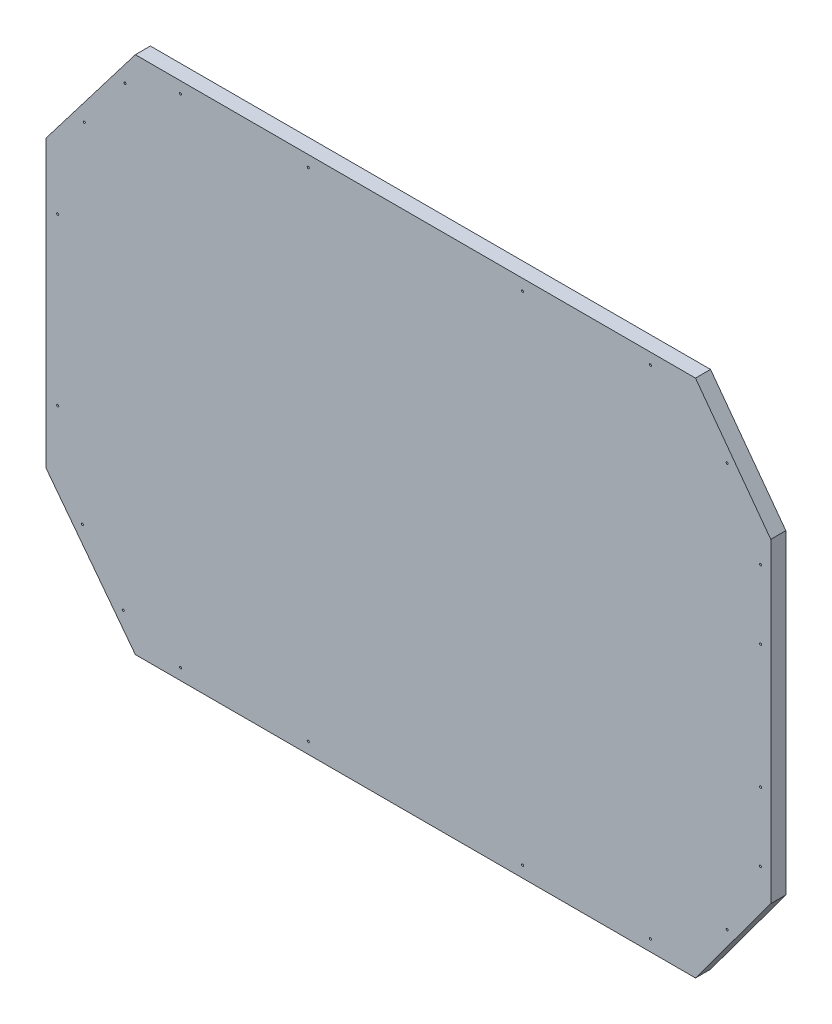
SolidWorks part; units mm, degrees
ref_plane "Front Plane" through (0, 0, 0) normal (0, 0, 1) x (1, 0, 0)
ref_plane "Top Plane" through (0, 0, 0) normal (0, 1, 0) x (1, 0, 0)
ref_plane "Right Plane" through (0, 0, 0) normal (1, 0, 0) x (0, 0, -1)
sketch "Sketch1" plane through (0, 0, 0) normal (0, 0, 1) x (1, 0, 0)
  line L0 (462.7979, 1011.4632) -> (442.7979, 1011.4632) construction
  line L1 (462.7979, 1036.4632) -> (462.7979, 1011.4632) construction
  line L2 (442.7979, 1036.4632) -> (442.7979, 1011.4632) construction
  line L3 (25, 700.8752) -> (25, 680.8752) construction
  line L4 (0, 700.8752) -> (25, 700.8752) construction
  line L5 (0, 680.8752) -> (25, 680.8752) construction
  line L6 (439.5826, 345.4877) -> (439.5826, 370.4877) construction
  line L7 (439.5826, 370.4877) -> (459.5826, 370.4877) construction
  line L8 (459.5826, 345.4877) -> (459.5826, 370.4877) construction
  line L9 (0, 500.6804) -> (118.58, 345.4877) construction
  line L10 (0, 881.2704) -> (0, 500.6804) construction
  line L11 (118.58, 1036.4632) -> (0, 881.2704) construction
  line L12 (863.58, 1036.4632) -> (118.58, 1036.4632) construction
  line L13 (863.58, 1036.4632) -> (963.71, 900.8043) construction
  line L14 (963.71, 900.8043) -> (963.71, 481.1465) construction
  line L15 (963.71, 481.1465) -> (863.58, 345.4877) construction
  line L16 (118.58, 345.4877) -> (863.58, 345.4877) construction
  line L17 (462.7979, 1011.4632) -> (442.7979, 1011.4632)
  line L18 (462.7979, 1036.4632) -> (462.7979, 1011.4632)
  line L19 (442.7979, 1036.4632) -> (442.7979, 1011.4632)
  line L20 (25, 700.8752) -> (25, 680.8752)
  line L21 (0, 700.8752) -> (25, 700.8752)
  line L22 (0, 680.8752) -> (25, 680.8752)
  line L23 (439.5826, 345.4877) -> (439.5826, 370.4877)
  line L24 (439.5826, 370.4877) -> (459.5826, 370.4877)
  line L25 (459.5826, 345.4877) -> (459.5826, 370.4877)
  line L26 (0, 500.6804) -> (118.58, 345.4877)
  line L27 (0, 881.2704) -> (0, 500.6804)
  line L28 (118.58, 1036.4632) -> (0, 881.2704)
  line L29 (863.58, 1036.4632) -> (118.58, 1036.4632)
  line L30 (863.58, 1036.4632) -> (963.71, 900.8043)
  line L31 (963.71, 900.8043) -> (963.71, 481.1465)
  line L32 (963.71, 481.1465) -> (863.58, 345.4877)
  line L33 (118.58, 345.4877) -> (863.58, 345.4877)
  circle A0 centre (905.6543, 422.2697) radius 1.5 construction
  circle A1 centre (950.0195, 517.2209) radius 1.5 construction
  circle A2 centre (950.0195, 608.6349) radius 1.5 construction
  circle A3 centre (950.0195, 773.3269) radius 1.5 construction
  circle A4 centre (905.6543, 959.6921) radius 1.5 construction
  circle A5 centre (950.0195, 864.7409) radius 1.5 construction
  circle A6 centre (803.58, 1021.4632) radius 1.5 construction
  circle A7 centre (633.58, 1021.4632) radius 1.5 construction
  circle A8 centre (348.58, 1021.4632) radius 1.5 construction
  circle A9 centre (178.58, 1021.4632) radius 1.5 construction
  circle A10 centre (104.8856, 996.6922) radius 1.5 construction
  circle A11 centre (50.7, 924.8318) radius 1.5 construction
  circle A12 centre (15.3287, 801.2704) radius 1.5 construction
  circle A13 centre (15.3287, 580.6804) radius 1.5 construction
  circle A14 centre (48.2964, 460.3067) radius 1.5 construction
  circle A15 centre (102.482, 388.4463) radius 1.5 construction
  circle A16 centre (178.58, 360.4877) radius 1.5 construction
  circle A17 centre (348.58, 360.4877) radius 1.5 construction
  circle A18 centre (803.58, 360.4877) radius 1.5 construction
  circle A19 centre (633.58, 360.4877) radius 1.5 construction
  circle A20 centre (905.6543, 422.2697) radius 1.5
  circle A21 centre (950.0195, 517.2209) radius 1.5
  circle A22 centre (950.0195, 608.6349) radius 1.5
  circle A23 centre (950.0195, 773.3269) radius 1.5
  circle A24 centre (905.6543, 959.6921) radius 1.5
  circle A25 centre (950.0195, 864.7409) radius 1.5
  circle A26 centre (803.58, 1021.4632) radius 1.5
  circle A27 centre (633.58, 1021.4632) radius 1.5
  circle A28 centre (348.58, 1021.4632) radius 1.5
  circle A29 centre (178.58, 1021.4632) radius 1.5
  circle A30 centre (104.8856, 996.6922) radius 1.5
  circle A31 centre (50.7, 924.8318) radius 1.5
  circle A32 centre (15.3287, 801.2704) radius 1.5
  circle A33 centre (15.3287, 580.6804) radius 1.5
  circle A34 centre (48.2964, 460.3067) radius 1.5
  circle A35 centre (102.482, 388.4463) radius 1.5
  circle A36 centre (178.58, 360.4877) radius 1.5
  circle A37 centre (348.58, 360.4877) radius 1.5
  circle A38 centre (803.58, 360.4877) radius 1.5
  circle A39 centre (633.58, 360.4877) radius 1.5
  point P80 (0, 0)
sketch "Sketch3" plane through (0, 0, 0) normal (0, 0, 1) x (1, 0, 0)
  line L0 (462.7979, 1011.4632) -> (442.7979, 1011.4632) construction
  line L1 (442.7979, 1036.4632) -> (442.7979, 1011.4632) construction
  line L2 (462.7979, 1036.4632) -> (462.7979, 1011.4632) construction
  line L3 (439.5826, 370.4877) -> (459.5826, 370.4877) construction
  line L4 (459.5826, 345.4877) -> (459.5826, 370.4877) construction
  line L5 (439.5826, 345.4877) -> (439.5826, 370.4877) construction
  line L6 (0, 680.8752) -> (25, 680.8752) construction
  line L7 (25, 700.8752) -> (25, 680.8752) construction
  line L8 (0, 700.8752) -> (25, 700.8752) construction
  line L9 (462.7979, 1011.4632) -> (442.7979, 1011.4632)
  line L10 (442.7979, 1036.4632) -> (442.7979, 1011.4632)
  line L11 (462.7979, 1036.4632) -> (462.7979, 1011.4632)
  line L12 (439.5826, 370.4877) -> (459.5826, 370.4877)
  line L13 (459.5826, 345.4877) -> (459.5826, 370.4877)
  line L14 (439.5826, 345.4877) -> (439.5826, 370.4877)
  line L15 (0, 680.8752) -> (25, 680.8752)
  line L16 (25, 700.8752) -> (25, 680.8752)
  line L17 (0, 700.8752) -> (25, 700.8752)
  circle A0 centre (633.58, 1021.4632) radius 1.5 construction
  circle A1 centre (633.58, 1021.4632) radius 1.5
  point P0 (442.7979, 1011.4632)
  point P2 (348.58, 1021.4632)
  point P4 (803.58, 1021.4632)
  point P6 (905.6543, 959.6921)
  point P8 (950.0195, 864.7409)
  point P10 (950.0195, 773.3269)
  point P12 (950.0195, 608.6349)
  point P14 (950.0195, 517.2209)
  point P16 (905.6543, 422.2697)
  point P18 (803.58, 360.4877)
  point P20 (633.58, 360.4877)
  point P22 (459.5826, 370.4877)
  point P24 (348.58, 360.4877)
  point P26 (178.58, 360.4877)
  point P28 (102.482, 388.4463)
  point P30 (48.2964, 460.3067)
  point P32 (15.3287, 580.6804)
  point P34 (15.3287, 801.2704)
  point P36 (50.7, 924.8318)
  point P38 (104.8856, 996.6922)
  point P40 (178.58, 1021.4632)
extrude "Boss-Extrude2" add sketch "Sketch1" along normal blind 20 contours L26 L33 L32 L31 L30 L29 L28 L27
sketch "Sketch8" plane through (0, 0, 0) normal (0, 0, -1) x (-1, 0, 0)
  line L0 (-442.7979, 1036.4632) -> (-442.7979, 1011.4632) construction
  line L1 (-462.7979, 1011.4632) -> (-442.7979, 1011.4632) construction
  line L2 (-462.7979, 1036.4632) -> (-462.7979, 1011.4632) construction
  line L3 (0, 680.8752) -> (-25, 680.8752) construction
  line L4 (-25, 700.8752) -> (-25, 680.8752) construction
  line L5 (0, 700.8752) -> (-25, 700.8752) construction
  line L6 (-459.5826, 345.4877) -> (-459.5826, 370.4877) construction
  line L7 (-439.5826, 370.4877) -> (-459.5826, 370.4877) construction
  line L8 (-439.5826, 345.4877) -> (-439.5826, 370.4877) construction
  line L9 (-442.7979, 1036.4632) -> (-442.7979, 1011.4632)
  line L10 (-462.7979, 1011.4632) -> (-442.7979, 1011.4632)
  line L11 (-462.7979, 1036.4632) -> (-462.7979, 1011.4632)
  line L12 (0, 680.8752) -> (-25, 680.8752)
  line L13 (-25, 700.8752) -> (-25, 680.8752)
  line L14 (0, 700.8752) -> (-25, 700.8752)
  line L15 (-459.5826, 345.4877) -> (-459.5826, 370.4877)
  line L16 (-439.5826, 370.4877) -> (-459.5826, 370.4877)
  line L17 (-439.5826, 345.4877) -> (-439.5826, 370.4877)
  circle A1 centre (-633.58, 1021.4632) radius 1.5
  circle A2 centre (-633.58, 1021.4632) radius 1.5
  dimension "D1" = 0
hole_wizard "CSK for #3 Flat Head Machine Screw (100)2" positions "Sketch9" profile "Sketch10" countersink size "#3" standard "ANSI Inch" end condition up to next
sketch "Sketch9" plane through (0, 0, 0) normal (0, 0, -1) x (-1, 0, 0)
  point P0 (-950.0195, 864.7409)
  point P3 (-950.0195, 773.3269)
  point P6 (-950.0195, 608.6349)
  point P9 (-950.0195, 517.2209)
  point P12 (-905.6543, 422.2697)
  point P15 (-803.58, 360.4877)
  point P18 (-633.58, 360.4877)
  point P21 (-348.58, 360.4877)
  point P24 (-178.58, 360.4877)
  point P27 (-102.482, 388.4463)
  point P30 (-48.2964, 460.3067)
  point P33 (-15.3287, 580.6804)
  point P36 (-15.3287, 801.2704)
  point P39 (-50.7, 924.8318)
  point P42 (-104.8856, 996.6922)
  point P45 (-178.58, 1021.4632)
  point P48 (-348.58, 1021.4632)
  point P51 (-633.58, 1021.4632)
  point P54 (-803.58, 1021.4632)
  point P57 (-905.6543, 959.6921)
sketch "Sketch10" plane through (950.0195, 864.7409, 0) normal (1, 0, 0) x (0, 1, 0)
  line L0 (0, 0) -> (0, 20)
  line L1 (0, 20) -> (1.397, 20)
  line L2 (1.397, 20) -> (1.397, 0.9484)
  line L3 (1.397, 0.9484) -> (2.5273, 0)
  line L5 (2.5273, 0) -> (0, 0)
  line L6 (-1.397, 0.9484) -> (-2.5273, 0) construction
  line L11 (0, -6.35) -> (0, 107.95) construction
  dimension "Thru Hole Dia." = 2.794
  dimension "Thru Hole Depth" = 20
  dimension "Near C'Sink Dia." = 5.0546
  dimension "Near C'Sink Angle" = 100
